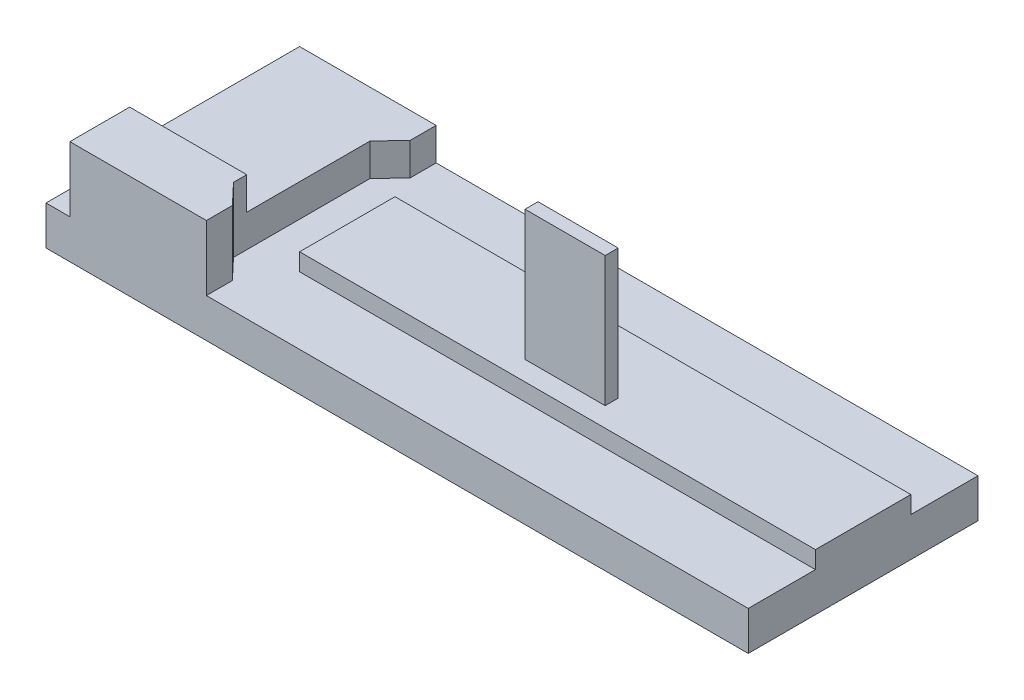
SolidWorks part; units mm, degrees
ref_plane "前视基准面" through (0, 0, 0) normal (0, 0, 1) x (1, 0, 0)
ref_plane "上视基准面" through (0, 0, 0) normal (0, 1, 0) x (1, 0, 0)
ref_plane "右视基准面" through (0, 0, 0) normal (1, 0, 0) x (0, 0, -1)
other "Configuration Table"
sketch "草图1" plane through (0, 0, 0) normal (0, 1, 0) x (1, 0, 0)
  line L1 (-81, -26.5) -> (81, -26.5)
  line L2 (-81, -26.5) -> (-81, 26.5)
  line L3 (-81, 26.5) -> (81, 26.5)
  line L4 (81, -26.5) -> (81, 26.5)
  line L5 (-81, -26.5) -> (81, 26.5) construction
  line L6 (-81, 26.5) -> (81, -26.5) construction
  point P0 (0, 0)
  dimension "D1" = 162
  dimension "D2" = 53
extrude "凸台-拉伸1" add sketch "草图1" along normal blind 9
sketch "草图2" plane through (0, 9, 0) normal (0, 1, 0) x (1, 0, 0)
  line L0 (-75.5, 26.5) -> (-75.5, -26.5)
  line L1 (81, 26.5) -> (-81, 26.5) construction
  line L2 (-81, -26.5) -> (81, -26.5) construction
  line L6 (-48.5, -15.75) -> (-48.5, 15.75)
  line L7 (-48.5, 15.75) -> (-44, 20.5)
  line L8 (-44, 20.5) -> (-44, 26.5)
  line L9 (-44, 26.5) -> (-75.5, 26.5)
  line L10 (-81, 26.5) -> (-81, -26.5) construction
  line L11 (0, 0) -> (90.88, 0) construction
  line L12 (-48.5, -15.75) -> (-44, -20.5)
  line L13 (-44, -20.5) -> (-44, -26.5)
  line L14 (-44, -26.5) -> (-75.5, -26.5)
  point P9 (-52.5771, 15.8066)
  point P16 (-54.9144, 21.483)
  point P17 (0, 0)
  point P19 (-52.3884, 15.75)
  point P20 (-44, 19.9193)
  point P21 (-50.3232, 12.6345)
  point P22 (-36.0488, 29.4132)
  dimension "D1" = 5.5
  dimension "D2" = 31.5
  dimension "D3" = 27
  dimension "D4" = 31.5
  dimension "D5" = 6
extrude "凸台-拉伸2" add sketch "草图2" along normal blind 15
sketch "草图5" plane through (-75.5, 0, 0) normal (-1, 0, 0) x (0, 0, 1)
  line L0 (-26.5, 24) -> (26.5, 24) construction
  line L1 (12.6969, 24) -> (-26.5, 24)
  line L2 (12.6969, 24) -> (12.6969, 16.5)
  line L3 (12.6969, 16.5) -> (-26.5, 16.5)
  line L4 (-26.5, 24) -> (-26.5, 16.5)
  line L5 (-26.5, 24) -> (-26.5, 9) construction
extrude "切除-拉伸1" cut sketch "草图5" against normal through all
sketch "草图6" plane through (-75.5, 0, 0) normal (-1, 0, 0) x (0, 0, 1)
  line L0 (19.5985, 24) -> (19.5985, -2.906) construction
  circle A0 centre (19.5985, 16.5176) radius 3.25
  dimension "D1" = 6.5
extrude "切除-拉伸2" cut sketch "草图6" against normal blind 15
sketch "草图7" plane through (0, 9, 0) normal (0, 1, 0) x (1, 0, 0)
  line L0 (81, -26.5) -> (81, 26.5) construction
  line L1 (81, 11) -> (-38, 11)
  line L2 (81, 11) -> (81, -11)
  line L3 (81, -11) -> (-38, -11)
  line L4 (-38, 11) -> (-38, -11)
  line L5 (0, 0) -> (127.3779, 0) construction
  point P7 (81, 16.7282)
  dimension "D1" = 22
  dimension "D2" = 119
extrude "凸台-拉伸3" add sketch "草图7" along normal blind 4
sketch "草图8" plane through (0, 13, 0) normal (0, 1, 0) x (1, 0, 0)
  line L0 (81, -11) -> (81, 11) construction
  line L1 (9.5, -3.5) -> (28, -3.5)
  line L2 (9.5, -3.5) -> (9.5, -6.5)
  line L3 (9.5, -6.5) -> (28, -6.5)
  line L4 (28, -3.5) -> (28, -6.5)
  line L5 (-44, -26.5) -> (81, -26.5) construction
  point P8 (0, 0)
  point P9 (12.3379, -3.5)
  point P10 (11.4578, -3.5)
  dimension "D1" = 53
  dimension "D2" = 20
  dimension "D3" = 3
  dimension "D4" = 18.5
extrude "凸台-拉伸4" add sketch "草图8" along normal blind 30
